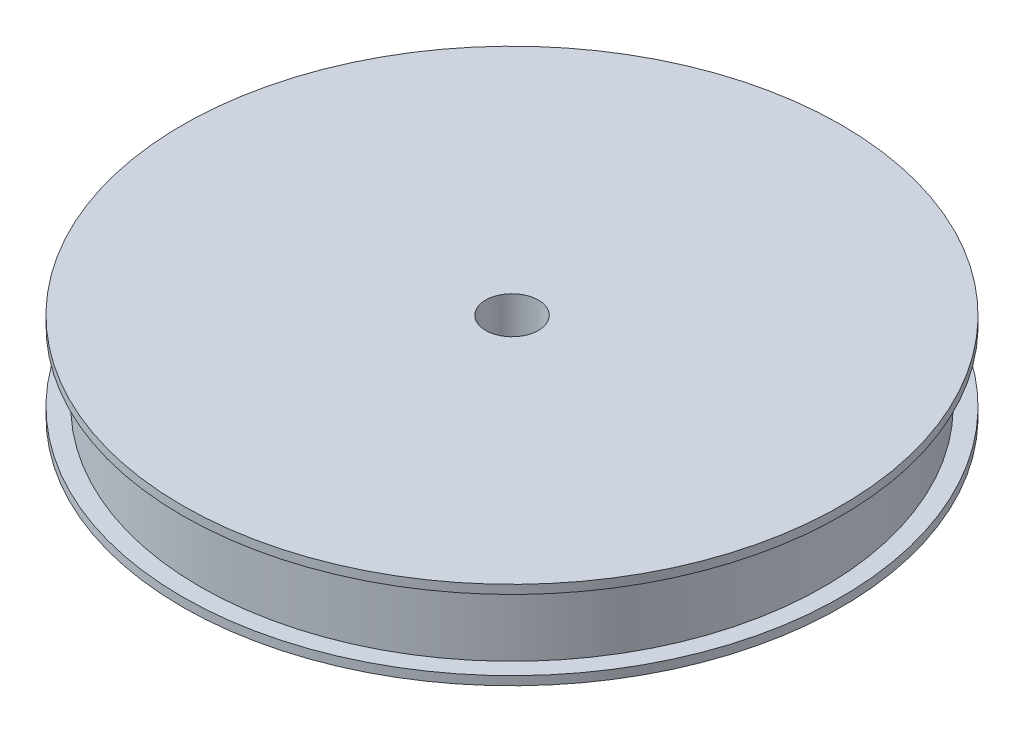
SolidWorks part; units mm, degrees
ref_plane "Front Plane" through (0, 0, 0) normal (0, 0, 1) x (1, 0, 0)
ref_plane "Top Plane" through (0, 0, 0) normal (0, 1, 0) x (1, 0, 0)
ref_plane "Right Plane" through (0, 0, 0) normal (1, 0, 0) x (0, 0, -1)
sketch "Sketch1" plane through (0, 0, 0) normal (0, 0, 1) x (1, 0, 0)
  line L0 (0, 14.3944) -> (0, -11.8534) construction
  line L1 (18.2757, 0) -> (-18.7366, 0) construction
  line L2 (-13.1465, 2.5) -> (-18.75, 2.5)
  line L3 (-18.75, 2.5) -> (-18.75, 2)
  line L4 (-18.75, 2) -> (-17.75, 2)
  line L5 (-17.75, 2) -> (-17.75, 0)
  line L6 (-13.1465, 2.5) -> (-1.5, 2.5)
  line L7 (-1.5, 2.5) -> (-1.5, 0)
  line L8 (-1.5, 0) -> (-17.75, 0)
  dimension "D1" = 1.5
  dimension "D2" = 18.75
  dimension "D3" = 1
  dimension "D4" = 2.5
  dimension "D5" = 0.5
revolve "Revolve1" add sketch "Sketch1" angle 360 about L0
mirror "Mirror1" of "Revolve1"
